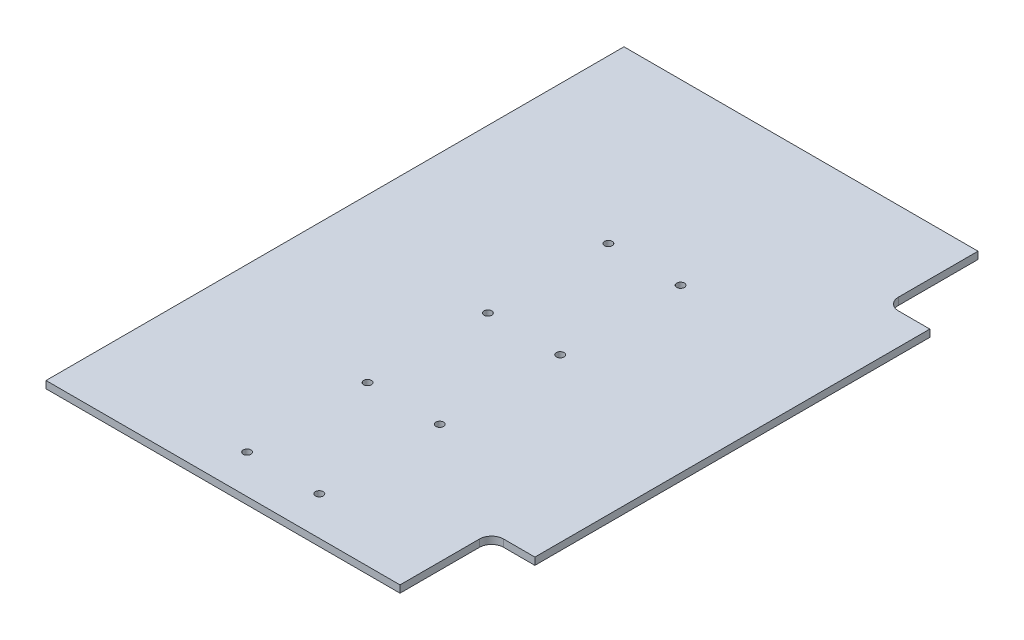
SolidWorks part; units mm, degrees
ref_plane "Front Plane" through (0, 0, 0) normal (0, 0, 1) x (1, 0, 0)
ref_plane "Top Plane" through (0, 0, 0) normal (0, 1, 0) x (1, 0, 0)
ref_plane "Right Plane" through (0, 0, 0) normal (1, 0, 0) x (0, 0, -1)
sketch "Sketch1" plane through (0, 0, 0) normal (0, 1, 0) x (1, 0, 0)
  line L1 (-82.5, 120) -> (82.5, 120)
  line L2 (-82.5, 120) -> (-82.5, -120)
  line L3 (-82.5, -120) -> (82.5, -120)
  line L4 (82.5, 120) -> (82.5, -120)
  line L5 (-82.5, 120) -> (82.5, -120) construction
  line L6 (-82.5, -120) -> (82.5, 120) construction
  point P0 (0, 0)
  dimension "D1" = 240
  dimension "D2" = 165
extrude "Boss-Extrude1" add sketch "Sketch1" along normal blind 3
sketch "Sketch3" plane through (0, 3, 0) normal (0, 1, 0) x (1, 0, 0)
  line L0 (0, 0) -> (0, -120) construction
  line L1 (-82.5, -120) -> (82.5, -120) construction
  line L2 (0, 0) -> (82.5, 0) construction
  line L3 (82.5, -120) -> (82.5, 120) construction
  line L4 (82.5, 120) -> (-82.5, 120) construction
  line L5 (15, 120) -> (-15, 120) construction
  line L6 (15, 120) -> (15, 46) construction
  line L7 (15, 46) -> (-15, 46) construction
  line L8 (-15, 120) -> (-15, 46) construction
  line L9 (0, 46) -> (0, 120) construction
  line L10 (15, 83) -> (-15, 83) construction
  circle A0 centre (15, 46) radius 1.6
  circle A1 centre (-15, 46) radius 1.6
  circle A2 centre (15, -4) radius 1.6
  circle A3 centre (-15, -4) radius 1.6
  circle A4 centre (15, -54) radius 1.6
  circle A5 centre (-15, -54) radius 1.6
  circle A6 centre (15, -104) radius 1.6
  circle A7 centre (-15, -104) radius 1.6
  point P172 (0, 83)
  dimension "D1" = 30
  dimension "D3" = 3.2
  dimension "D4" = 4
  dimension "D2" = 74
  dimension "D5" = 50
extrude "Cut-Extrude2" cut sketch "Sketch3" against normal blind 11
sketch "Sketch2" plane through (0, 3, 0) normal (0, 1, 0) x (1, 0, 0)
  line L0 (0, 0) -> (82.5, 0) construction
  line L1 (82.5, 120) -> (64.5, 120)
  line L2 (82.5, 120) -> (82.5, 82)
  line L3 (82.5, 82) -> (64.5, 82)
  line L4 (64.5, 120) -> (64.5, 82)
  line L5 (73.5, 82) -> (73.5, 120) construction
  line L6 (82.5, 101) -> (64.5, 101) construction
  line L7 (82.5, -120) -> (82.5, 120) construction
  line L8 (82.5, -82) -> (64.5, -82)
  line L9 (64.5, -120) -> (64.5, -82)
  line L10 (82.5, -120) -> (64.5, -120)
  line L11 (82.5, -120) -> (82.5, -82)
  point P148 (73.5, 101)
  dimension "D1" = 38
  dimension "D2" = 18
extrude "Cut-Extrude1" cut sketch "Sketch2" against normal blind 11
fillet "Fillet1" radius 5 2 edges at (64.5, 1.5, 82) (64.5, 1.5, -82)
